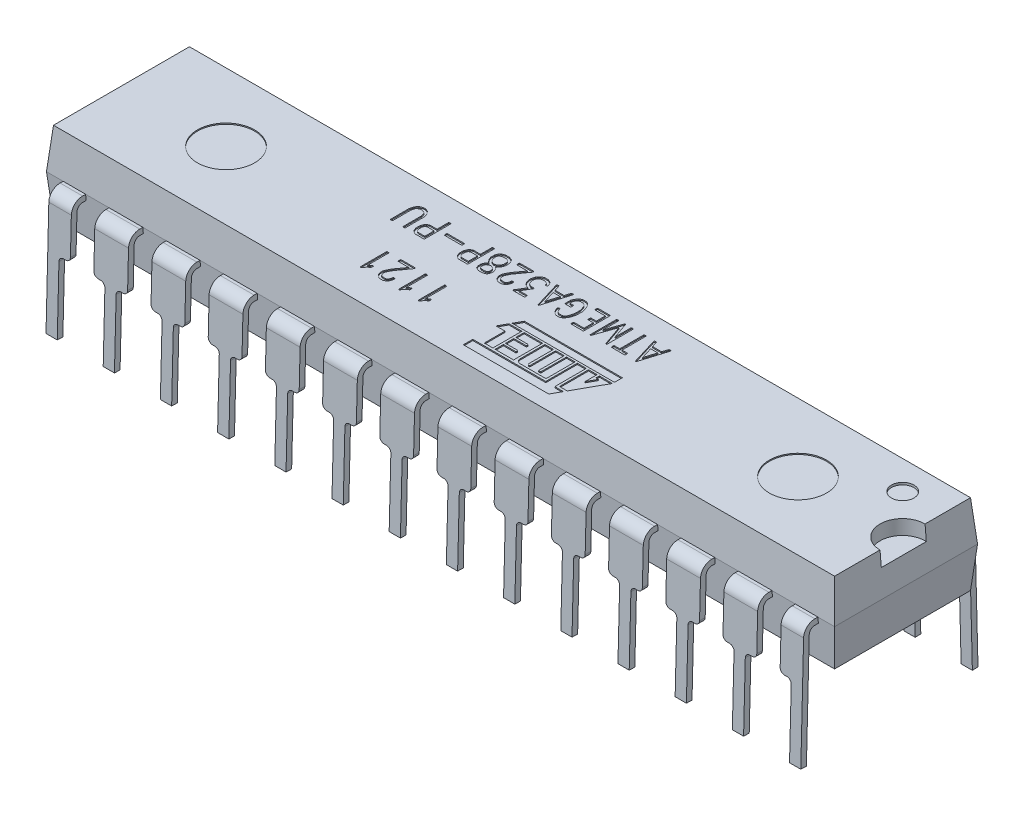
SolidWorks part; units mm, degrees
material "Pure Silver"
ref_plane "Front Plane" through (0, 0, 0) normal (0, 0, 1) x (1, 0, 0)
ref_plane "Top Plane" through (0, 0, 0) normal (0, 1, 0) x (1, 0, 0)
ref_plane "Right Plane" through (0, 0, 0) normal (1, 0, 0) x (0, 0, -1)
sketch "Sketch1" plane through (0, 0, 0) normal (1, 0, 0) x (0, 0, -1)
  line L0 (-3.935, -3.18) -> (-3.81, 1.8075)
  line L1 (-3.3102, 2.295) -> (3.3102, 2.295)
  line L2 (3.81, 1.8075) -> (3.935, -3.18)
  line L4 (55, 0) -> (-55, 0) construction
  line L5 (0, 4.893) -> (0, -4.893) construction
  arc A0 (3.3102, 2.295) -> (3.81, 1.8075) centre (3.3102, 1.795) cw
  arc A1 (-3.81, 1.8075) -> (-3.3102, 2.295) centre (-3.3102, 1.795) cw
  dimension "D1" = 0.5
  dimension "D2" = 7.62
  dimension "D3" = 3.81
  dimension "D4" = 3.18
  dimension "D5" = 2.295
  dimension "D6" = 7.87
  dimension "D7" = 3.935
extrude "Extrude-Thin1" add sketch "Sketch1" along normal mid plane 33.52 thin
sketch "Sketch2" plane through (0, 0, 0) normal (0, 0, 1) x (1, 0, 0)
  line L0 (-3.56, -3.5) -> (-3.56, -0.2)
  line L1 (-6.1, -3.5) -> (-6.1, -0.2)
  line L2 (4.3285, 0) -> (-4.3285, 0) construction
  line L3 (-1.52, -0.2) -> (-1.52, -3.5)
  line L4 (-3.56, -3.5) -> (-1.52, -3.5)
  line L5 (-1.02, -3.5) -> (-1.02, -0.2)
  line L6 (1.02, -0.2) -> (1.02, -3.5)
  line L7 (-1.02, -3.5) -> (1.02, -3.5)
  line L8 (1.52, -3.5) -> (1.52, -0.2)
  line L9 (3.56, -0.2) -> (3.56, -3.5)
  line L10 (1.52, -3.5) -> (3.56, -3.5)
  line L11 (-4.06, -0.2) -> (-4.06, -3.5)
  line L12 (-5.9, 0) -> (-5.8, 0)
  line L13 (0, -3.0147) -> (0, 3.0147) construction
  line L14 (-3.36, 0) -> (-3.26, 0)
  line L15 (-3.06, 0.2) -> (-3.06, 2.295)
  line L16 (16.76, 2.295) -> (-16.76, 2.295) construction
  line L17 (-3.06, 2.295) -> (-2.02, 2.295)
  line L18 (-2.02, 2.295) -> (-2.02, 0.2)
  line L19 (-0.52, 0.2) -> (-0.52, 2.295)
  line L20 (-0.52, 2.295) -> (0.52, 2.295)
  line L21 (0.52, 2.295) -> (0.52, 0.2)
  line L22 (2.02, 0.2) -> (2.02, 2.295)
  line L23 (2.02, 2.295) -> (3.06, 2.295)
  line L24 (3.06, 2.295) -> (3.06, 0.2)
  line L25 (-5.6, 0.2) -> (-5.6, 2.295)
  line L26 (-1.82, 0) -> (-1.72, 0)
  line L27 (-4.56, 2.295) -> (-4.56, 0.2)
  line L28 (-0.82, 0) -> (-0.72, 0)
  line L29 (0.72, 0) -> (0.82, 0)
  line L30 (1.72, 0) -> (1.82, 0)
  line L31 (3.26, 0) -> (3.36, 0)
  line L32 (-4.36, 0) -> (-4.26, 0)
  line L33 (-5.6, 2.295) -> (-4.56, 2.295)
  line L34 (-6.1, -3.5) -> (-4.06, -3.5)
  line L35 (-8.64, -3.5) -> (-8.64, -0.2)
  line L36 (-6.6, -0.2) -> (-6.6, -3.5)
  line L37 (-8.44, 0) -> (-8.34, 0)
  line L38 (-8.14, 0.2) -> (-8.14, 2.295)
  line L39 (-7.1, 2.295) -> (-7.1, 0.2)
  line L40 (-6.9, 0) -> (-6.8, 0)
  line L41 (-8.14, 2.295) -> (-7.1, 2.295)
  line L42 (-8.64, -3.5) -> (-6.6, -3.5)
  line L43 (-11.18, -3.5) -> (-11.18, -0.2)
  line L44 (-9.14, -0.2) -> (-9.14, -3.5)
  line L45 (-10.98, 0) -> (-10.88, 0)
  line L46 (-10.68, 0.2) -> (-10.68, 2.295)
  line L47 (-9.64, 2.295) -> (-9.64, 0.2)
  line L48 (-9.44, 0) -> (-9.34, 0)
  line L49 (-10.68, 2.295) -> (-9.64, 2.295)
  line L50 (-11.18, -3.5) -> (-9.14, -3.5)
  line L51 (-13.72, -3.5) -> (-13.72, -0.2)
  line L52 (-11.68, -0.2) -> (-11.68, -3.5)
  line L53 (-13.52, 0) -> (-13.42, 0)
  line L54 (-13.22, 0.2) -> (-13.22, 2.295)
  line L55 (-12.18, 2.295) -> (-12.18, 0.2)
  line L56 (-11.98, 0) -> (-11.88, 0)
  line L57 (-13.22, 2.295) -> (-12.18, 2.295)
  line L58 (-13.72, -3.5) -> (-11.68, -3.5)
  line L59 (-16.26, -3.5) -> (-16.26, -0.2)
  line L60 (-14.22, -0.2) -> (-14.22, -3.5)
  line L61 (-16.06, 0) -> (-15.96, 0)
  line L62 (-15.76, 0.2) -> (-15.76, 2.295)
  line L63 (-14.72, 2.295) -> (-14.72, 0.2)
  line L64 (-14.52, 0) -> (-14.42, 0)
  line L65 (-15.76, 2.295) -> (-14.72, 2.295)
  line L66 (-16.26, -3.5) -> (-14.22, -3.5)
  line L67 (4.06, -3.5) -> (4.06, -0.2)
  line L68 (6.1, -0.2) -> (6.1, -3.5)
  line L69 (5.8, 0) -> (5.9, 0)
  line L70 (4.26, 0) -> (4.36, 0)
  line L71 (4.56, 0.2) -> (4.56, 2.295)
  line L72 (5.6, 2.295) -> (5.6, 0.2)
  line L73 (4.56, 2.295) -> (5.6, 2.295)
  line L74 (4.06, -3.5) -> (6.1, -3.5)
  line L75 (6.6, -3.5) -> (6.6, -0.2)
  line L76 (8.64, -0.2) -> (8.64, -3.5)
  line L77 (8.34, 0) -> (8.44, 0)
  line L78 (6.8, 0) -> (6.9, 0)
  line L79 (7.1, 0.2) -> (7.1, 2.295)
  line L80 (8.14, 2.295) -> (8.14, 0.2)
  line L81 (7.1, 2.295) -> (8.14, 2.295)
  line L82 (6.6, -3.5) -> (8.64, -3.5)
  line L83 (9.14, -3.5) -> (9.14, -0.2)
  line L84 (11.18, -0.2) -> (11.18, -3.5)
  line L85 (10.88, 0) -> (10.98, 0)
  line L86 (9.34, 0) -> (9.44, 0)
  line L87 (9.64, 0.2) -> (9.64, 2.295)
  line L88 (10.68, 2.295) -> (10.68, 0.2)
  line L89 (9.64, 2.295) -> (10.68, 2.295)
  line L90 (9.14, -3.5) -> (11.18, -3.5)
  line L91 (11.68, -3.5) -> (11.68, -0.2)
  line L92 (13.72, -0.2) -> (13.72, -3.5)
  line L93 (13.42, 0) -> (13.52, 0)
  line L94 (11.88, 0) -> (11.98, 0)
  line L95 (12.18, 0.2) -> (12.18, 2.295)
  line L96 (13.22, 2.295) -> (13.22, 0.2)
  line L97 (12.18, 2.295) -> (13.22, 2.295)
  line L98 (11.68, -3.5) -> (13.72, -3.5)
  line L99 (14.22, -3.5) -> (14.22, -0.2)
  line L100 (16.26, -0.2) -> (16.26, -3.5)
  line L101 (15.96, 0) -> (16.06, 0)
  line L102 (14.42, 0) -> (14.52, 0)
  line L103 (14.72, 0.2) -> (14.72, 2.295)
  line L104 (15.76, 2.295) -> (15.76, 0.2)
  line L105 (14.72, 2.295) -> (15.76, 2.295)
  line L106 (14.22, -3.5) -> (16.26, -3.5)
  line L107 (1.52, -3.5) -> (4.06, -3.5) construction
  arc A0 (-3.56, -0.2) -> (-3.36, 0) centre (-3.36, -0.2) cw
  arc A1 (-1.52, -0.2) -> (-1.72, 0) centre (-1.72, -0.2) ccw
  arc A2 (-1.02, -0.2) -> (-0.82, 0) centre (-0.82, -0.2) cw
  arc A3 (3.56, -0.2) -> (3.36, 0) centre (3.36, -0.2) ccw
  arc A4 (1.52, -0.2) -> (1.72, 0) centre (1.72, -0.2) cw
  arc A5 (1.02, -0.2) -> (0.82, 0) centre (0.82, -0.2) ccw
  arc A6 (-3.26, 0) -> (-3.06, 0.2) centre (-3.26, 0.2) ccw
  arc A7 (-2.02, 0.2) -> (-1.82, 0) centre (-1.82, 0.2) ccw
  arc A8 (3.06, 0.2) -> (3.26, 0) centre (3.26, 0.2) ccw
  arc A9 (2.02, 0.2) -> (1.82, 0) centre (1.82, 0.2) cw
  arc A10 (0.52, 0.2) -> (0.72, 0) centre (0.72, 0.2) ccw
  arc A11 (-0.52, 0.2) -> (-0.72, 0) centre (-0.72, 0.2) cw
  arc A12 (-6.1, -0.2) -> (-5.9, 0) centre (-5.9, -0.2) cw
  arc A13 (-5.8, 0) -> (-5.6, 0.2) centre (-5.8, 0.2) ccw
  arc A14 (-4.56, 0.2) -> (-4.36, 0) centre (-4.36, 0.2) ccw
  arc A15 (-4.06, -0.2) -> (-4.26, 0) centre (-4.26, -0.2) ccw
  arc A16 (-8.64, -0.2) -> (-8.44, 0) centre (-8.44, -0.2) cw
  arc A17 (-8.34, 0) -> (-8.14, 0.2) centre (-8.34, 0.2) ccw
  arc A18 (-7.1, 0.2) -> (-6.9, 0) centre (-6.9, 0.2) ccw
  arc A19 (-6.6, -0.2) -> (-6.8, 0) centre (-6.8, -0.2) ccw
  arc A20 (-11.18, -0.2) -> (-10.98, 0) centre (-10.98, -0.2) cw
  arc A21 (-10.88, 0) -> (-10.68, 0.2) centre (-10.88, 0.2) ccw
  arc A22 (-9.64, 0.2) -> (-9.44, 0) centre (-9.44, 0.2) ccw
  arc A23 (-9.14, -0.2) -> (-9.34, 0) centre (-9.34, -0.2) ccw
  arc A24 (-13.72, -0.2) -> (-13.52, 0) centre (-13.52, -0.2) cw
  arc A25 (-13.42, 0) -> (-13.22, 0.2) centre (-13.42, 0.2) ccw
  arc A26 (-12.18, 0.2) -> (-11.98, 0) centre (-11.98, 0.2) ccw
  arc A27 (-11.68, -0.2) -> (-11.88, 0) centre (-11.88, -0.2) ccw
  arc A28 (-16.26, -0.2) -> (-16.06, 0) centre (-16.06, -0.2) cw
  arc A29 (-15.96, 0) -> (-15.76, 0.2) centre (-15.96, 0.2) ccw
  arc A30 (-14.72, 0.2) -> (-14.52, 0) centre (-14.52, 0.2) ccw
  arc A31 (-14.22, -0.2) -> (-14.42, 0) centre (-14.42, -0.2) ccw
  arc A32 (6.1, -0.2) -> (5.9, 0) centre (5.9, -0.2) ccw
  arc A33 (5.6, 0.2) -> (5.8, 0) centre (5.8, 0.2) ccw
  arc A34 (4.56, 0.2) -> (4.36, 0) centre (4.36, 0.2) cw
  arc A35 (4.06, -0.2) -> (4.26, 0) centre (4.26, -0.2) cw
  arc A36 (8.64, -0.2) -> (8.44, 0) centre (8.44, -0.2) ccw
  arc A37 (8.14, 0.2) -> (8.34, 0) centre (8.34, 0.2) ccw
  arc A38 (7.1, 0.2) -> (6.9, 0) centre (6.9, 0.2) cw
  arc A39 (6.6, -0.2) -> (6.8, 0) centre (6.8, -0.2) cw
  arc A40 (11.18, -0.2) -> (10.98, 0) centre (10.98, -0.2) ccw
  arc A41 (10.68, 0.2) -> (10.88, 0) centre (10.88, 0.2) ccw
  arc A42 (9.64, 0.2) -> (9.44, 0) centre (9.44, 0.2) cw
  arc A43 (9.14, -0.2) -> (9.34, 0) centre (9.34, -0.2) cw
  arc A44 (13.72, -0.2) -> (13.52, 0) centre (13.52, -0.2) ccw
  arc A45 (13.22, 0.2) -> (13.42, 0) centre (13.42, 0.2) ccw
  arc A46 (12.18, 0.2) -> (11.98, 0) centre (11.98, 0.2) cw
  arc A47 (11.68, -0.2) -> (11.88, 0) centre (11.88, -0.2) cw
  arc A48 (16.26, -0.2) -> (16.06, 0) centre (16.06, -0.2) ccw
  arc A49 (15.76, 0.2) -> (15.96, 0) centre (15.96, 0.2) ccw
  arc A50 (14.72, 0.2) -> (14.52, 0) centre (14.52, 0.2) cw
  arc A51 (14.22, -0.2) -> (14.42, 0) centre (14.42, -0.2) cw
  point P35 (-3.56, 0)
  point P40 (-1.52, 0)
  point P43 (-1.02, 0)
  point P46 (3.56, 0)
  point P49 (1.52, 0)
  point P52 (1.02, 0)
  point P55 (-3.06, 0)
  point P58 (-2.02, 0)
  point P61 (3.06, 0)
  point P64 (2.02, 0)
  point P67 (0.52, 0)
  point P70 (-0.52, 0)
  dimension "D7" = 0.2
  dimension "D1" = 0.5
  dimension "D2" = 2.54
  dimension "D3" = 1.52
  dimension "D4" = 1.52
  dimension "D5" = 1.5
  dimension "D6" = 0.5
  dimension "D8" = 3.5
  dimension "D10" = 4.56
  dimension "D12" = 2.54
  dimension "D9" = 6
  dimension "D11" = 6
extrude "Cut-Extrude1" cut sketch "Sketch2" against normal through all and the other way through all
sketch "Sketch3" plane through (0, 0, 0) normal (1, 0, 0) x (0, 0, -1)
  line L0 (0, 4.893) -> (0, -4.893) construction
  line L1 (-3.0188, 4.08) -> (3.0188, 4.08)
  line L2 (-3.3102, 2.295) -> (3.3102, 2.295) construction
  line L3 (-3.0188, 0.51) -> (3.0188, 0.51)
  line L5 (4.3285, 0) -> (-4.3285, 0) construction
  line L6 (-3.175, 2.295) -> (-3.0188, 4.08)
  line L7 (-3.175, 2.295) -> (-3.0188, 0.51)
  line L8 (3.0188, 4.08) -> (3.175, 2.295)
  line L9 (3.175, 2.295) -> (3.0188, 0.51)
  dimension "D1" = 85
  dimension "D2" = 6.35
  dimension "D3" = 4.08
  dimension "D4" = 0.51
  dimension "D5" = 85
  dimension "D6" = 3.175
  dimension "D7" = 3.57
extrude "Boss-Extrude1" add sketch "Sketch3" along normal mid plane 35
sketch "Sketch4" plane through (0, 0, 0) normal (0, 0, 1) x (1, 0, 0)
  line L0 (-17.3438, 4.08) -> (-17.5, 2.295)
  line L1 (17.5, 4.08) -> (-17.5, 4.08) construction
  line L2 (-17.5, 2.295) -> (-17.3438, 0.51)
  line L3 (17.5, 0.51) -> (-17.5, 0.51) construction
  line L4 (17.5, 2.295) -> (17.3438, 4.08)
  line L5 (17.5, 2.295) -> (17.3438, 0.51)
  line L6 (0, -3.0147) -> (0, 3.0147) construction
  line L7 (17.3438, 4.08) -> (20, 4.08)
  line L8 (20, 4.08) -> (20, 0.51)
  line L9 (20, 0.51) -> (17.3438, 0.51)
  line L11 (-17.3438, 4.08) -> (-20, 4.08)
  line L12 (-20, 4.08) -> (-20, 0.51)
  line L13 (-20, 0.51) -> (-17.3438, 0.51)
  dimension "D1" = 5
  dimension "D2" = 5
  dimension "D3" = 40
  dimension "D4" = 20
extrude "Cut-Extrude2" cut sketch "Sketch4" against normal through all and the other way through all
sketch "Sketch5" plane through (0, 4.08, 0) normal (0, 1, 0) x (1, 0, 0)
  line L0 (17.3438, 3.0188) -> (17.3438, -3.0188) construction
  circle A0 centre (17.3438, 0) radius 1
  dimension "D1" = 2
extrude "Cut-Extrude3" cut sketch "Sketch5" against normal blind 0.65
sketch "Sketch6" plane through (0, 4.08, 0) normal (0, 1, 0) x (1, 0, 0)
  line L0 (0.4051, -0.54) -> (0.98, -0.54)
  line L1 (5, -0.45) -> (0.455, -0.45)
  line L2 (0.649, -0.1) -> (0.455, -0.45)
  line L3 (1.08, -0.91) -> (1.61, -0.91)
  line L4 (0.2, -0.91) -> (0.6, -0.91)
  line L5 (1.08, -1) -> (1.61, -1)
  line L6 (1.08, -1.37) -> (1.61, -1.37)
  line L7 (1.08, -1.46) -> (1.61, -1.46)
  line L8 (0.2, -1.94) -> (3.44, -1.94)
  line L9 (0.2, -2.36) -> (3.9912, -2.36)
  line L10 (5, -0.54) -> (4.2849, -1.83)
  line L11 (2.2, -1.83) -> (3.34, -1.83)
  line L12 (4.42, -0.54) -> (4.42, -0.69)
  line L13 (0.649, -0.1) -> (5, -0.1)
  line L14 (5, -0.1) -> (5, -0.45)
  line L15 (4.42, -0.69) -> (4.53, -0.69)
  line L16 (4.53, -0.69) -> (4.32, -1.0689)
  line L17 (4.32, -1.0689) -> (4.32, -0.54)
  line L18 (0.98, -0.54) -> (0.98, -1.83)
  line L19 (1.08, -0.54) -> (1.08, -1.83)
  line L20 (1.9, -0.54) -> (1.9, -1.83)
  line L21 (2, -0.54) -> (2, -1.63)
  line L22 (2.38, -0.54) -> (2.38, -1.63)
  line L23 (2.48, -0.54) -> (2.48, -1.69)
  line L24 (2.86, -0.54) -> (2.86, -1.67)
  line L25 (2.96, -0.54) -> (2.96, -1.67)
  line L26 (3.34, -0.54) -> (3.34, -1.83)
  line L27 (3.44, -0.54) -> (3.44, -1.94)
  line L28 (3.84, -0.54) -> (3.84, -1.94)
  line L29 (3.94, -0.54) -> (3.94, -1.83)
  line L30 (2.94, -1.69) -> (2.88, -1.69)
  line L31 (2.48, -1.69) -> (2.44, -1.69)
  line L32 (1.9, -1.83) -> (1.08, -1.83)
  line L33 (0.6, -0.91) -> (0.6, -1.83)
  line L34 (0.4051, -0.54) -> (0.2, -0.91)
  line L35 (1.64, -0.94) -> (1.64, -0.97)
  line L36 (3.94, -1.83) -> (4.2849, -1.83)
  line L37 (3.84, -1.94) -> (4.224, -1.94)
  line L38 (1.08, -0.54) -> (1.9, -0.54)
  line L39 (2, -0.54) -> (2.38, -0.54)
  line L40 (1.64, -1.4) -> (1.64, -1.43)
  line L41 (0.98, -1.83) -> (0.6, -1.83)
  line L42 (0.2, -1.94) -> (0.2, -2.36)
  line L43 (4.224, -1.94) -> (3.9912, -2.36)
  line L44 (2.48, -0.54) -> (2.86, -0.54)
  line L45 (2.96, -0.54) -> (3.34, -0.54)
  line L46 (3.44, -0.54) -> (3.84, -0.54)
  line L47 (3.94, -0.54) -> (4.32, -0.54)
  line L48 (4.42, -0.54) -> (5, -0.54)
  line L49 (0, -3.9964) -> (0, 3.9964) construction
  line L55 (-4.893, 0) -> (4.893, 0) construction
  arc A0 (2.2, -1.83) -> (2, -1.63) centre (2.2, -1.63) cw
  arc A1 (2.44, -1.69) -> (2.38, -1.63) centre (2.44, -1.63) cw
  arc A2 (2.94, -1.69) -> (2.96, -1.67) centre (2.94, -1.67) ccw
  arc A3 (2.86, -1.67) -> (2.88, -1.69) centre (2.88, -1.67) ccw
  arc A4 (1.61, -1.46) -> (1.64, -1.43) centre (1.61, -1.43) ccw
  arc A5 (1.64, -1.4) -> (1.61, -1.37) centre (1.61, -1.4) ccw
  arc A6 (1.61, -1) -> (1.64, -0.97) centre (1.61, -0.97) ccw
  arc A7 (1.64, -0.94) -> (1.61, -0.91) centre (1.61, -0.94) ccw
  dimension "D25" = 0.2
  dimension "D26" = 0.06
  dimension "D28" = 0.02
  dimension "D33" = 0.03
  dimension "D1" = 0.09
  dimension "D2" = 0.09
  dimension "D3" = 0.09
  dimension "D4" = 0.11
  dimension "D5" = 61
  dimension "D6" = 0.15
  dimension "D7" = 0.11
  dimension "D8" = 0.37
  dimension "D9" = 0.37
  dimension "D10" = 0.37
  dimension "D11" = 0.42
  dimension "D12" = 0.1
  dimension "D13" = 0.1
  dimension "D14" = 0.1
  dimension "D15" = 0.1
  dimension "D16" = 0.1
  dimension "D17" = 0.1
  dimension "D18" = 1.06
  dimension "D19" = 0.4
  dimension "D20" = 0.38
  dimension "D21" = 0.38
  dimension "D22" = 0.38
  dimension "D23" = 0.82
  dimension "D24" = 4.8
  dimension "D27" = 0.14
  dimension "D29" = 0.38
  dimension "D30" = 0.38
  dimension "D31" = 0.1
  dimension "D32" = 0.56
  dimension "D34" = 5
  dimension "D36" = 0.35
  dimension "D37" = 0.1
extrude "Cut-Extrude4" cut sketch "Sketch6" against normal blind 0.05 contours L46 L27 L8 L42 L9 L43 L37 L28 | A3 L24 L44 L23 L31 A1 L22 L39 L21 A0 L11 L26 L45 L25 A2 L30 | L48 L12 L15 L16 L17 L47 L29 L36 L10 | A7 L35 A6 L5 L19 L6 A5 L40 A4 L7 L32 L20 L38 L3 | L41 L18 L0 L34 L4 L33 | L13 L14 L1 L2
sketch "Sketch8" plane through (0, 4.08, 0) normal (0, 1, 0) x (1, 0, 0)
  line L0 (-2, -0.5) -> (-6.7038, -0.5) construction
  line L1 (5.1, 2) -> (-7.2875, 2) construction
  line L2 (-4.893, 0) -> (4.893, 0) construction
  line L3 (0, -3.9964) -> (0, 3.9964) construction
  text T0 "1121" font "SWRomnd" height 1.2
  text T1 "ATMEGA328P-PU" font "SWRomnd" height 1.2
  dimension "D1" = 2
  dimension "D2" = 0.5
  dimension "D3" = 2
  dimension "D4" = 5.1
extrude "Cut-Extrude5" cut sketch "Sketch8" against normal blind 0.05
sketch "Sketch9" plane through (0, 4.08, 0) normal (0, 1, 0) x (1, 0, 0)
  line L0 (-4.893, 0) -> (4.893, 0) construction
  line L1 (0, -3.9964) -> (0, 3.9964) construction
  circle A0 centre (-12.7, 0) radius 1.27
  circle A1 centre (12.7, 0) radius 1.27
  dimension "D1" = 2.54
  dimension "D2" = 12.7
  dimension "D3" = 12.7
extrude "Cut-Extrude6" cut sketch "Sketch9" against normal blind 0.05
sketch "Sketch10" plane through (0, 4.08, 0) normal (0, 1, 0) x (1, 0, 0)
  line L0 (0, -3.9964) -> (0, 3.9964) construction
  line L1 (-4.893, 0) -> (4.893, 0) construction
  circle A0 centre (15.6, 1.75) radius 0.5
  point P6 (13.6638, 2.8044)
  dimension "D1" = 1
  dimension "D2" = 15.6
  dimension "D3" = 1.75
extrude "Cut-Extrude7" cut sketch "Sketch10" against normal blind 0.1
